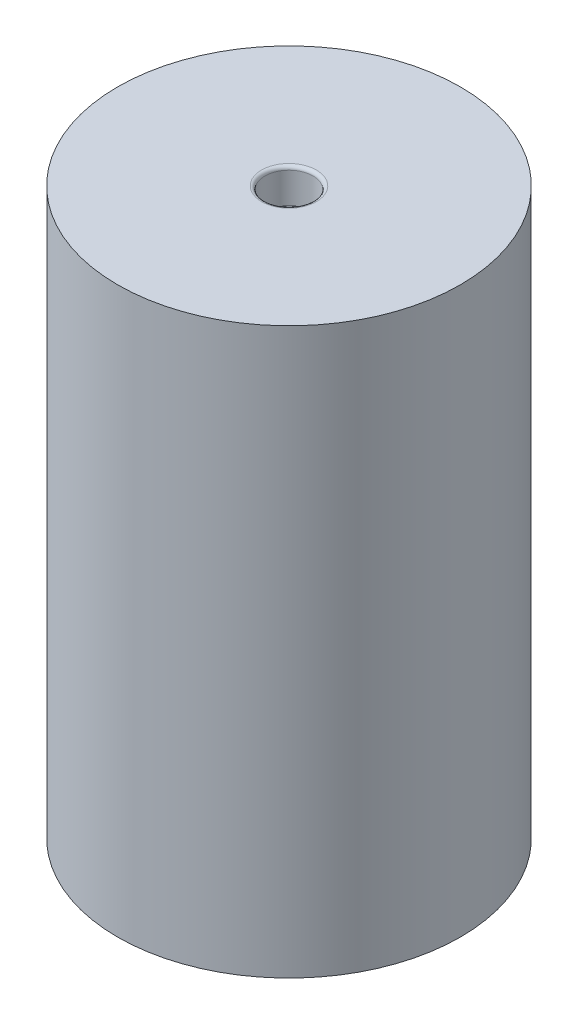
SolidWorks part; units mm, degrees
ref_plane "Front Plane" through (0, 0, 0) normal (0, 0, 1) x (1, 0, 0)
ref_plane "Top Plane" through (0, 0, 0) normal (0, 1, 0) x (1, 0, 0)
ref_plane "Right Plane" through (0, 0, 0) normal (1, 0, 0) x (0, 0, -1)
sketch "Sketch1" plane through (0, 0, 0) normal (0, 1, 0) x (1, 0, 0)
  circle A0 centre (0, 0) radius 25
  dimension "D1" = 50
extrude "Boss-Extrude1" add sketch "Sketch1" along normal blind 82.4
sketch "Sketch2" plane through (0, 82.4, 0) normal (0, 1, 0) x (1, 0, 0)
  circle A0 centre (0, 0) radius 3.5
  dimension "D1" = 7
extrude "Cut-Extrude1" cut sketch "Sketch2" against normal blind 5
sketch "Sketch3" plane through (0, 0, 0) normal (0, -1, 0) x (1, 0, 0)
  circle A0 centre (0, 0) radius 3.5
  dimension "D1" = 7
extrude "Cut-Extrude2" cut sketch "Sketch3" against normal blind 5
fillet "Fillet1" radius 0.5 2 edges at (0, 82.4, 3.5) (0, 0, -3.5)
